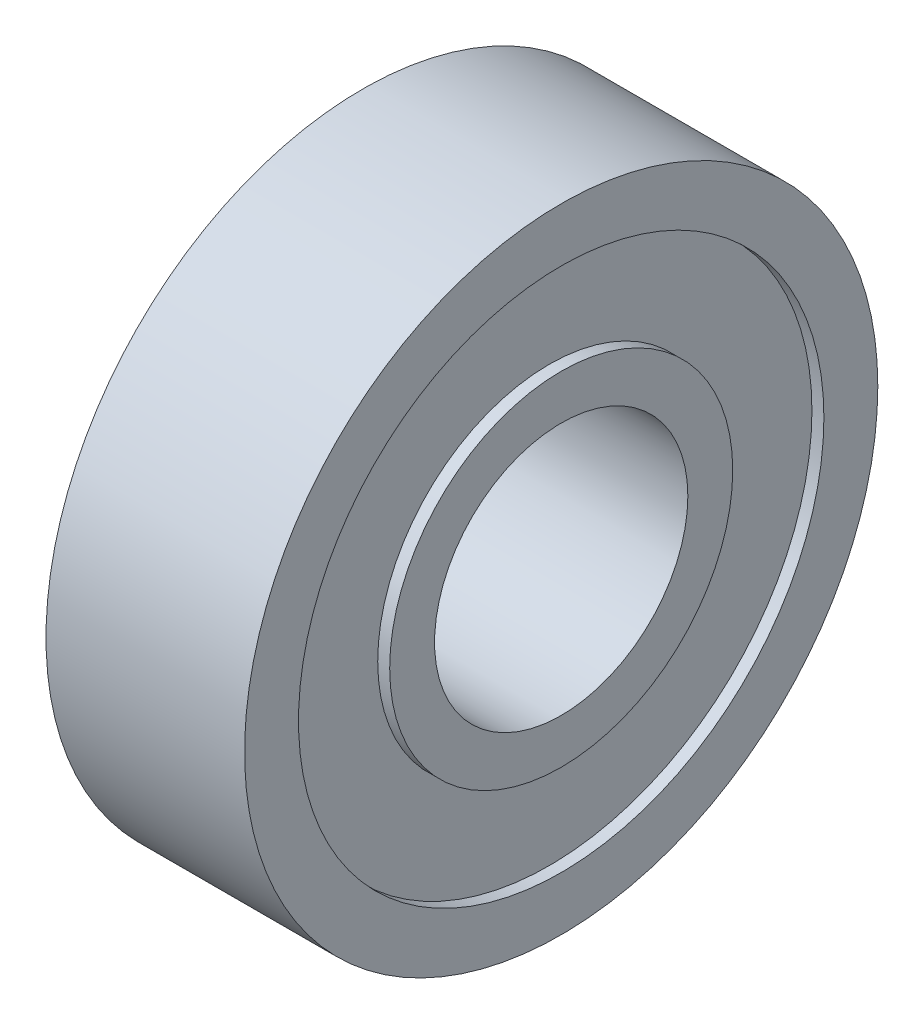
SolidWorks part; units mm, degrees
material "Plain Carbon Steel"
ref_plane "Front Plane" through (0, 0, 0) normal (0, 0, 1) x (1, 0, 0)
ref_plane "Top Plane" through (0, 0, 0) normal (0, 1, 0) x (1, 0, 0)
ref_plane "Right Plane" through (0, 0, 0) normal (1, 0, 0) x (0, 0, -1)
sketch "Sketch1" plane through (0, 0, 0) normal (0, 0, 1) x (1, 0, 0)
  line L0 (2.4892, 3.175) -> (-2.4892, 3.175)
  line L1 (-2.4892, 3.175) -> (-2.4892, 4.3)
  line L2 (-2.4892, 4.3) -> (-2.1892, 4.3)
  line L3 (-2.1892, 4.3) -> (-2.1892, 6.586)
  line L4 (-2.1892, 6.586) -> (-2.4892, 6.586)
  line L5 (-2.4892, 6.586) -> (-2.4892, 7.9375)
  line L6 (-2.4892, 7.9375) -> (2.4892, 7.9375)
  line L7 (0, 7.9375) -> (0, 3.175) construction
  line L8 (2.4892, 6.586) -> (2.4892, 7.9375)
  line L9 (2.1892, 6.586) -> (2.4892, 6.586)
  line L10 (2.1892, 4.3) -> (2.1892, 6.586)
  line L11 (2.4892, 4.3) -> (2.1892, 4.3)
  line L12 (2.4892, 3.175) -> (2.4892, 4.3)
  line L13 (0, 0) -> (-4.3663, 0) construction
  dimension "D1" = 6.35
  dimension "D2" = 15.875
  dimension "D3" = 4.9784
  dimension "D4" = 8.6
  dimension "D5" = 2.286
  dimension "D6" = 0.3
revolve "Revolve1" add sketch "Sketch1" angle 360 about L13
